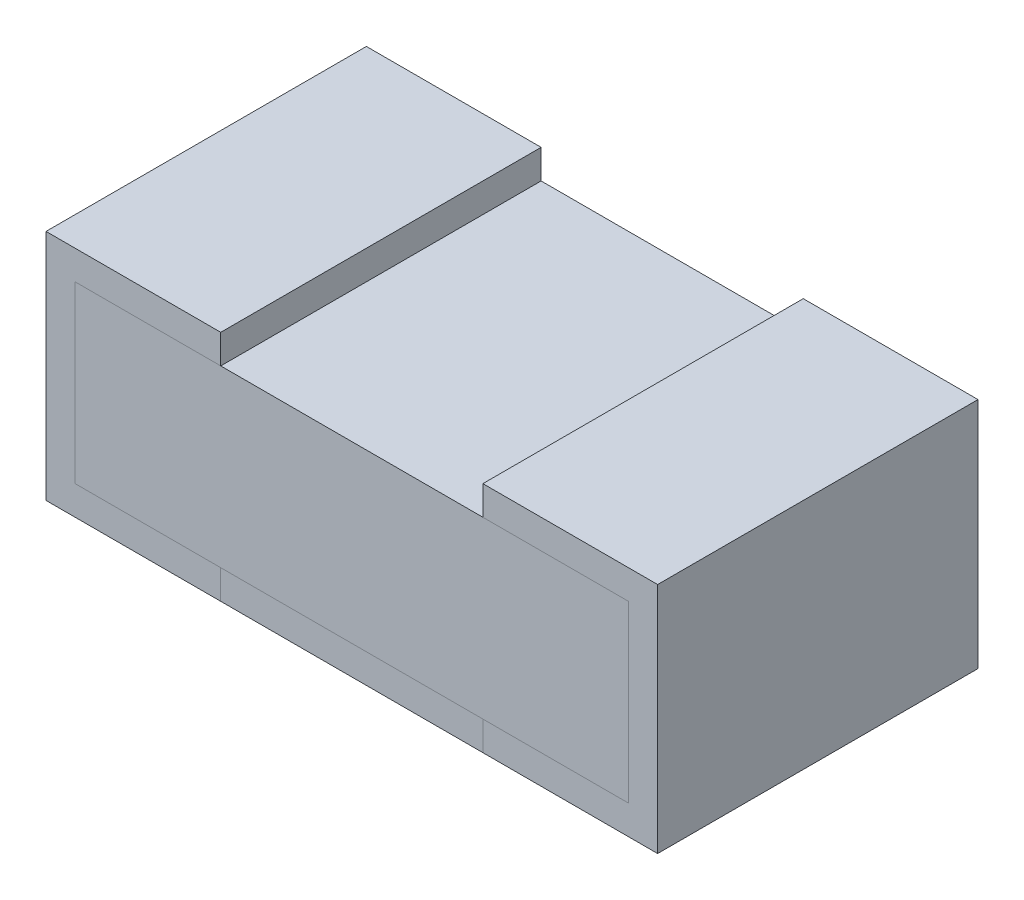
SolidWorks part; units mm, degrees
ref_plane "Front Plane" through (0, 0, 0) normal (0, 0, 1) x (1, 0, 0)
ref_plane "Top Plane" through (0, 0, 0) normal (0, 1, 0) x (1, 0, 0)
ref_plane "Right Plane" through (0, 0, 0) normal (1, 0, 0) x (0, 0, -1)
sketch "Szkic1" plane through (0, 0, 0) normal (0, 0, 1) x (1, 0, 0)
  line L0 (0.3, 0.05) -> (0.05, 0.05)
  line L1 (0.05, 0.05) -> (0.05, 0.35)
  line L2 (0.05, 0.35) -> (0.3, 0.35)
  line L3 (0.3, 0.35) -> (0.3, 0.4)
  line L4 (0.3, 0.4) -> (0, 0.4)
  line L5 (0, 0.4) -> (0, 0)
  line L6 (0, 0) -> (0.3, 0)
  line L7 (0.3, 0) -> (0.3, 0.05)
  line L11 (0.75, 0.35) -> (1, 0.35)
  line L12 (1, 0.35) -> (1, 0.05)
  line L13 (1, 0.05) -> (0.75, 0.05)
  line L14 (0.75, 0.05) -> (0.75, 0)
  line L15 (0.75, 0) -> (1.05, 0)
  line L16 (1.05, 0) -> (1.05, 0.4)
  line L17 (1.05, 0.4) -> (0.75, 0.4)
  line L18 (0.75, 0.4) -> (0.75, 0.35)
extrude "Dodanie-wyciągnięcie1" add sketch "Szkic1" along normal blind 0.55
sketch "Szkic2" plane through (0, 0, 0.55) normal (0, 0, 1) x (1, 0, 0)
  line L0 (0.75, 0) -> (0.3, 0)
  line L1 (0.3, 0) -> (0.3, 0.05)
  line L2 (0.3, 0.05) -> (0.75, 0.05)
  line L3 (0.75, 0.05) -> (0.75, 0)
extrude "Dodanie-wyciągnięcie2" add sketch "Szkic2" against normal blind 0.55 separate body
sketch "Szkic3" plane through (0, 0, 0.55) normal (0, 0, 1) x (1, 0, 0)
  line L0 (1, 0.05) -> (0.05, 0.05)
  line L1 (0.05, 0.05) -> (0.05, 0.35) construction
  line L2 (0.05, 0.05) -> (0.05, 0.35)
  line L3 (0.05, 0.35) -> (1, 0.35)
  line L4 (1, 0.35) -> (1, 0.05)
extrude "Dodanie-wyciągnięcie3" add sketch "Szkic3" against normal blind 0.55 separate body
scale "Skala1" bodies to scale 102 104 103 101 scale about origin uniform scaling yes scale factor 2.5
